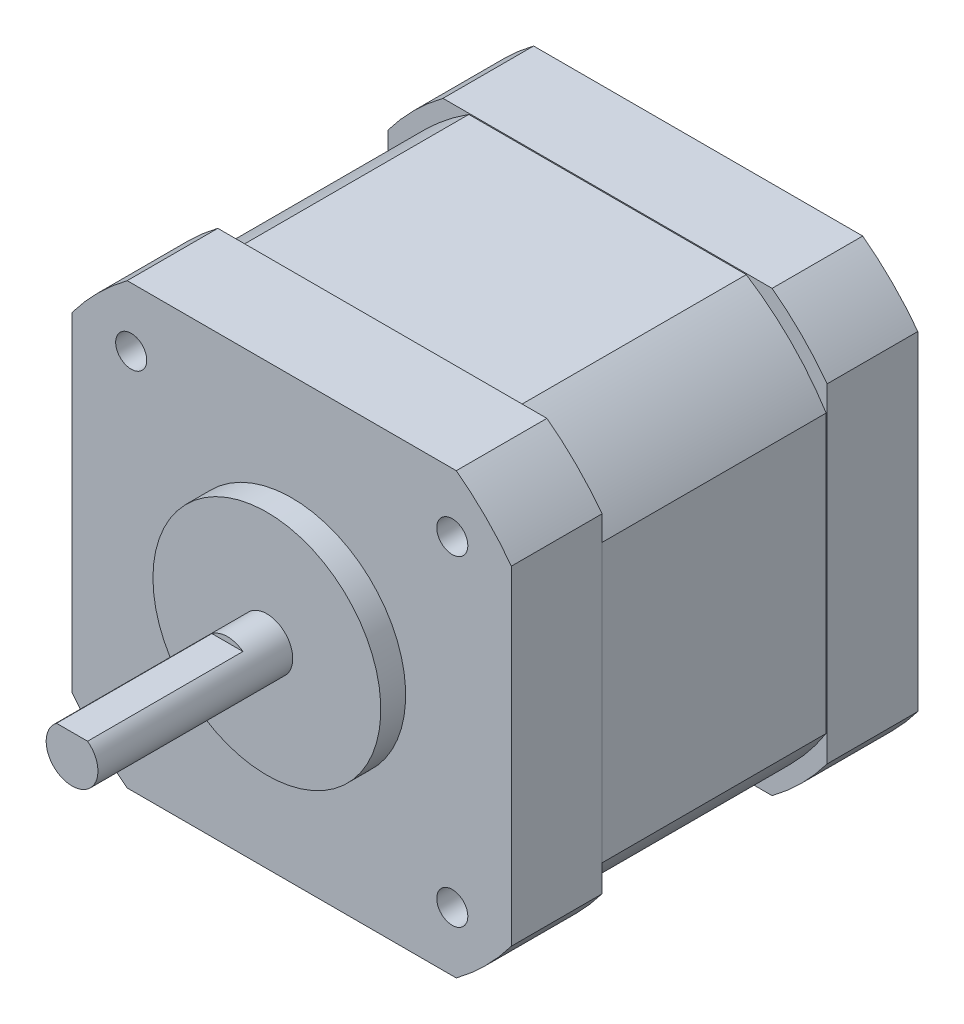
SolidWorks part; units mm, degrees
material "Plain Carbon Steel"
ref_plane "Front" through (0, 0, 0) normal (0, 0, 1) x (1, 0, 0)
ref_plane "Top" through (0, 0, 0) normal (0, 1, 0) x (1, 0, 0)
ref_plane "Right" through (0, 0, 0) normal (1, 0, 0) x (0, 0, -1)
sketch "Sketch1" plane through (0, 0, 0) normal (0, 0, 1) x (1, 0, 0)
  circle A0 centre (0, 0) radius 2.5
  dimension "D1" = 5
extrude "Boss-Extrude1" add sketch "Sketch1" along normal blind 21.21
sketch "Sketch2" plane through (0, 0, 0) normal (0, 0, -1) x (-1, 0, 0)
  circle A0 centre (0, 0) radius 11
  dimension "D1" = 22
extrude "Boss-Extrude2" add sketch "Sketch2" against normal blind 2.4
sketch "Sketch3" plane through (0, 0, 0) normal (0, 0, -1) x (-1, 0, 0)
  line L1 (21.209, -21.209) -> (-21.209, -21.209)
  line L2 (21.209, -21.209) -> (21.209, 21.209)
  line L3 (21.209, 21.209) -> (-21.209, 21.209)
  line L4 (-21.209, -21.209) -> (-21.209, 21.209)
  line L5 (21.209, -21.209) -> (-21.209, 21.209) construction
  line L6 (21.209, 21.209) -> (-21.209, -21.209) construction
  point P0 (0, 0)
  dimension "D1" = 42.418
extrude "Boss-Extrude3" add sketch "Sketch3" along normal blind 39.24
sketch "Sketch4" plane through (0, 0, -39.24) normal (0, 0, -1) x (-1, 0, 0)
  line L0 (-21.209, -15.888) -> (-21.209, -21.209)
  line L1 (15.888, -21.209) -> (21.209, -21.209)
  line L2 (21.209, 15.888) -> (21.209, 21.209)
  line L3 (-15.888, 21.209) -> (-21.209, 21.209)
  line L4 (-21.209, 21.209) -> (-21.209, -21.209)
  line L5 (-21.209, -21.209) -> (21.209, -21.209)
  line L6 (21.209, -21.209) -> (21.209, 21.209)
  line L7 (21.209, 21.209) -> (-21.209, 21.209)
  line L8 (-21.209, 21.209) -> (-21.209, 15.888)
  line L9 (-21.209, -21.209) -> (-15.888, -21.209)
  line L10 (21.209, -21.209) -> (21.209, -15.888)
  line L11 (21.209, 21.209) -> (15.888, 21.209)
  arc A0 (-21.209, -15.888) -> (-15.888, -21.209) centre (0, 0) ccw
  arc A1 (15.888, -21.209) -> (21.209, -15.888) centre (0, 0) ccw
  arc A2 (21.209, 15.888) -> (15.888, 21.209) centre (0, 0) ccw
  arc A3 (-15.888, 21.209) -> (-21.209, 15.888) centre (0, 0) ccw
  dimension "D2" = 26.5
  dimension "D1" = 0
extrude "Cut-Extrude1" cut sketch "Sketch4" against normal through all
hole_wizard "M3x0.5 Tapped Hole1" positions "Sketch6" profile "Sketch5" tap size "M3x0.5" standard "ANSI Metric"
sketch "Sketch6" plane through (0, 0, 0) normal (0, 0, 1) x (1, 0, 0)
  line L0 (-16.1632, 0) -> (0, 0) construction
  line L1 (0, 0) -> (0, 15.0764) construction
  point P0 (-15.5, 15.5)
  point P11 (-15.5, -15.5)
  point P12 (15.5, -15.5)
  point P13 (15.5, 15.5)
  dimension "D1" = 31
  dimension "D2" = 31
sketch "Sketch5" plane through (-15.5, 15.5, 0) normal (1, 0, 0) x (0, -1, 0)
  line L0 (0, 0) -> (0, 8.2511)
  line L1 (0, 8.2511) -> (1.25, 7.5)
  line L2 (1.25, 7.5) -> (1.25, 6)
  line L3 (1.25, 6) -> (1.5, 6)
  line L4 (1.5, 6) -> (1.5, 0)
  line L5 (1.5, 0) -> (0, 0)
  line L10 (0, 8.2511) -> (-1.25, 7.5) construction
  line L11 (0, -6.35) -> (0, 107.95) construction
  dimension "Tap Drill Dia." = 2.5
  dimension "Tap Drill Depth" = 7.5
  dimension "Thread Major Dia." = 3
  dimension "Thread Depth" = 6
  dimension "Drill Angle" = 118
sketch "Sketch7" plane through (0, 0, 21.21) normal (0, 0, 1) x (1, 0, 0)
  line L0 (-1.5, 2) -> (1.5, 2)
  circle A0 centre (0, 0) radius 2.5 construction
  circle A1 centre (0, 0) radius 2.5 construction
  arc A2 (1.5, 2) -> (-1.5, 2) centre (0, 0) ccw
  dimension "D1" = 4.5
extrude "Cut-Extrude2" cut sketch "Sketch7" against normal blind 15
ref_plane "Plane1" through (0, 0, -19.62) normal (0, 0, 1) x (1, 0, 0)
sketch "Sketch8" plane through (0, 0, -19.62) normal (0, 0, 1) x (1, 0, 0)
  line L0 (-13.3944, 21.109) -> (13.3944, 21.109)
  line L1 (-5.7152, 0) -> (0, 0) construction
  line L2 (0, 0) -> (0, 8.4579) construction
  line L3 (-15.888, 21.209) -> (15.888, 21.209) construction
  line L4 (-13.3944, -21.109) -> (13.3944, -21.109)
  line L5 (-21.109, 13.3944) -> (-21.109, -13.3944)
  line L6 (-21.209, -15.888) -> (-21.209, 15.888) construction
  line L7 (21.109, 13.3944) -> (21.109, -13.3944)
  line L12 (15.888, 21.209) -> (-15.888, 21.209)
  line L13 (-21.209, 15.888) -> (-21.209, -15.888)
  line L14 (-15.888, -21.209) -> (15.888, -21.209)
  line L15 (21.209, -15.888) -> (21.209, 15.888)
  line L16 (15.888, 21.209) -> (-15.888, 21.209)
  line L17 (-21.209, 15.888) -> (-21.209, -15.888)
  line L18 (-15.888, -21.209) -> (15.888, -21.209)
  line L19 (21.209, -15.888) -> (21.209, 15.888)
  arc A0 (-13.3944, 21.109) -> (-21.109, 13.3944) centre (0, 0) ccw
  arc A1 (-21.109, -13.3944) -> (-13.3944, -21.109) centre (0, 0) ccw
  arc A2 (21.109, 13.3944) -> (13.3944, 21.109) centre (0, 0) ccw
  arc A3 (13.3944, -21.109) -> (21.109, -13.3944) centre (0, 0) ccw
  arc A5 (-15.888, 21.209) -> (-21.209, 15.888) centre (0, 0) ccw
  arc A6 (-21.209, -15.888) -> (-15.888, -21.209) centre (0, 0) ccw
  arc A7 (15.888, -21.209) -> (21.209, -15.888) centre (0, 0) ccw
  arc A8 (21.209, 15.888) -> (15.888, 21.209) centre (0, 0) ccw
  arc A9 (-15.888, 21.209) -> (-21.209, 15.888) centre (0, 0) ccw
  arc A10 (-21.209, -15.888) -> (-15.888, -21.209) centre (0, 0) ccw
  arc A11 (15.888, -21.209) -> (21.209, -15.888) centre (0, 0) ccw
  arc A12 (21.209, 15.888) -> (15.888, 21.209) centre (0, 0) ccw
  dimension "D1" = 50
  dimension "D2" = 0.1
  dimension "D3" = 0.1
  dimension "D4" = 0
extrude "Cut-Extrude3" cut sketch "Sketch8" against normal mid plane 21.74
